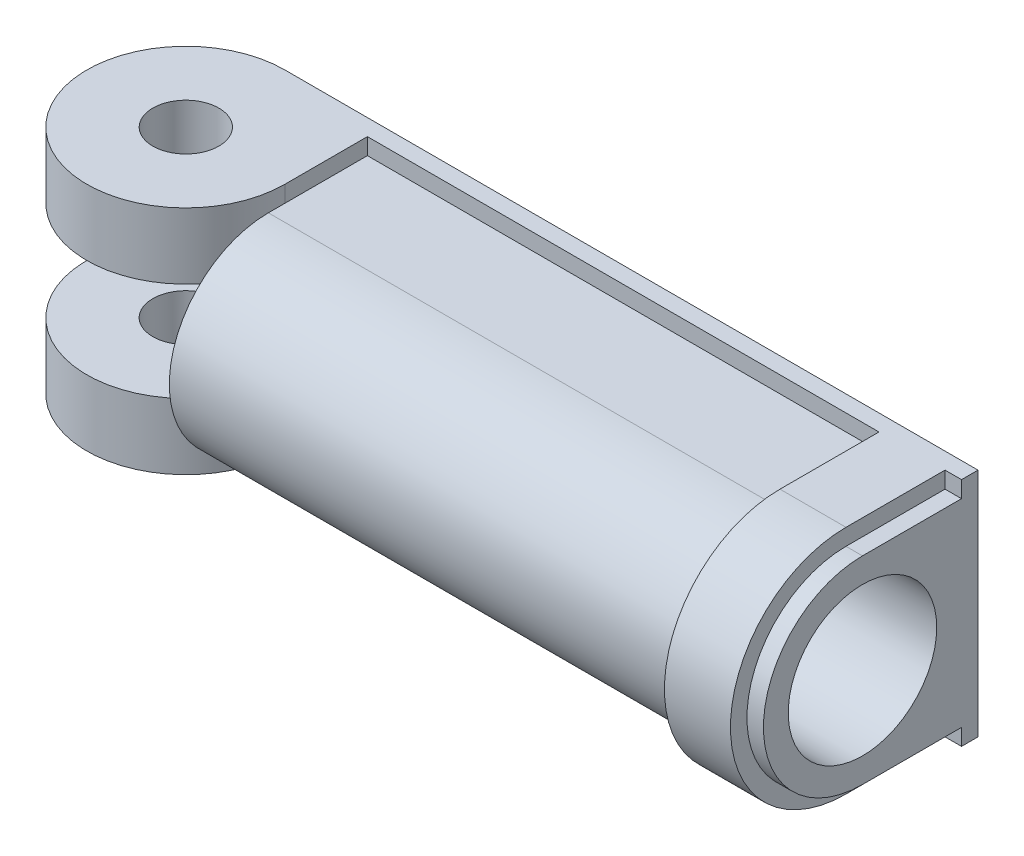
SolidWorks part; units mm, degrees
material "AISI 1035 Steel (SS)"
ref_plane "Front Plane" through (0, 0, 0) normal (0, 0, 1) x (1, 0, 0)
ref_plane "Top Plane" through (0, 0, 0) normal (0, 1, 0) x (1, 0, 0)
ref_plane "Right Plane" through (0, 0, 0) normal (1, 0, 0) x (0, 0, -1)
sketch "Sketch1" plane through (0, 0, 0) normal (1, 0, 0) x (0, 0, -1)
  line L1 (10.9779, 10.9779) -> (10.9779, -10.9779)
  line L2 (0, 9.4107) -> (9.4107, 9.4107)
  line L3 (0, -9.4107) -> (9.4107, -9.4107)
  line L4 (10.9779, 10.9779) -> (9.4107, 10.9779)
  line L5 (10.9779, -10.9779) -> (9.4107, -10.9779)
  line L6 (9.4107, 10.9779) -> (9.4107, 9.4107)
  line L7 (9.4107, -9.4107) -> (9.4107, -10.9779)
  arc A0 (0, 9.4107) -> (0, -9.4107) centre (0, 0) ccw
extrude "Boss-Extrude1" add sketch "Sketch1" against normal blind 56.4566
ref_plane "Plane1" through (-1.5672, 0, 0) normal (1, 0, 0) x (0, 0, -1)
sketch "Sketch3" plane through (-1.5672, 0, 0) normal (1, 0, 0) x (0, 0, -1)
  line L0 (9.4107, 10.9779) -> (0, 10.9779)
  line L1 (9.4107, -10.9779) -> (0, -10.9779)
  line L2 (9.4107, 10.9779) -> (9.4107, -10.9779)
  arc A0 (0, 10.9779) -> (0, -10.9779) centre (0, 0) ccw
extrude "Boss-Extrude2" add sketch "Sketch3" against normal blind 6.2738
sketch "Sketch4" plane through (0, 10.9779, 0) normal (0, 1, 0) x (1, 0, 0)
  line L0 (-56.4566, 10.9779) -> (-65.8673, 10.9779)
  line L1 (-56.4566, 1.5672) -> (-56.4566, 10.9779)
  arc A0 (-65.8673, 10.9779) -> (-56.4566, 1.5672) centre (-65.8673, 1.5672) ccw
extrude "Boss-Extrude3" add sketch "Sketch4" against normal blind 6.2738
mirror "Mirror1" about plane through (0, 0, 0) normal (0, 1, 0) of "Boss-Extrude3"
sketch "Sketch5" plane through (0, 10.9779, 0) normal (0, 1, 0) x (1, 0, 0)
  circle A0 centre (-65.8673, 1.5672) radius 3.1369
extrude "Cut-Extrude1" cut sketch "Sketch5" against normal through all
sketch "Sketch6" plane through (0, 0, 0) normal (1, 0, 0) x (0, 0, -1)
  circle A0 centre (0, 0) radius 7.0561
extrude "Cut-Extrude2" cut sketch "Sketch6" against normal blind 53.3197
sketch "Sketch7" plane through (0, 0, -10.9779) normal (0, 0, -1) x (-1, 0, 0)
  line L0 (65.8673, -10.9779) -> (0, -10.9779) construction
  line L1 (0, 10.9779) -> (53.3946, 10.9779)
  line L2 (0, 10.9779) -> (0, -10.9779)
  line L3 (0, -10.9779) -> (53.3946, -10.9779)
  line L4 (53.3946, 10.9779) -> (53.3946, -10.9779)
  line L5 (0, 3.8135) -> (8.5398, -10.9779)
  line L6 (4.7537, 10.9779) -> (17.4298, -10.9779)
  line L7 (13.6437, 10.9779) -> (26.3198, -10.9779)
  line L8 (22.5337, 10.9779) -> (35.2098, -10.9779)
  line L9 (31.4237, 10.9779) -> (44.0998, -10.9779)
  line L10 (40.3137, 10.9779) -> (52.9898, -10.9779)
  line L11 (49.2037, 10.9779) -> (53.3946, 3.719)
  dimension "D1" = 7
split line "Split Line1"
